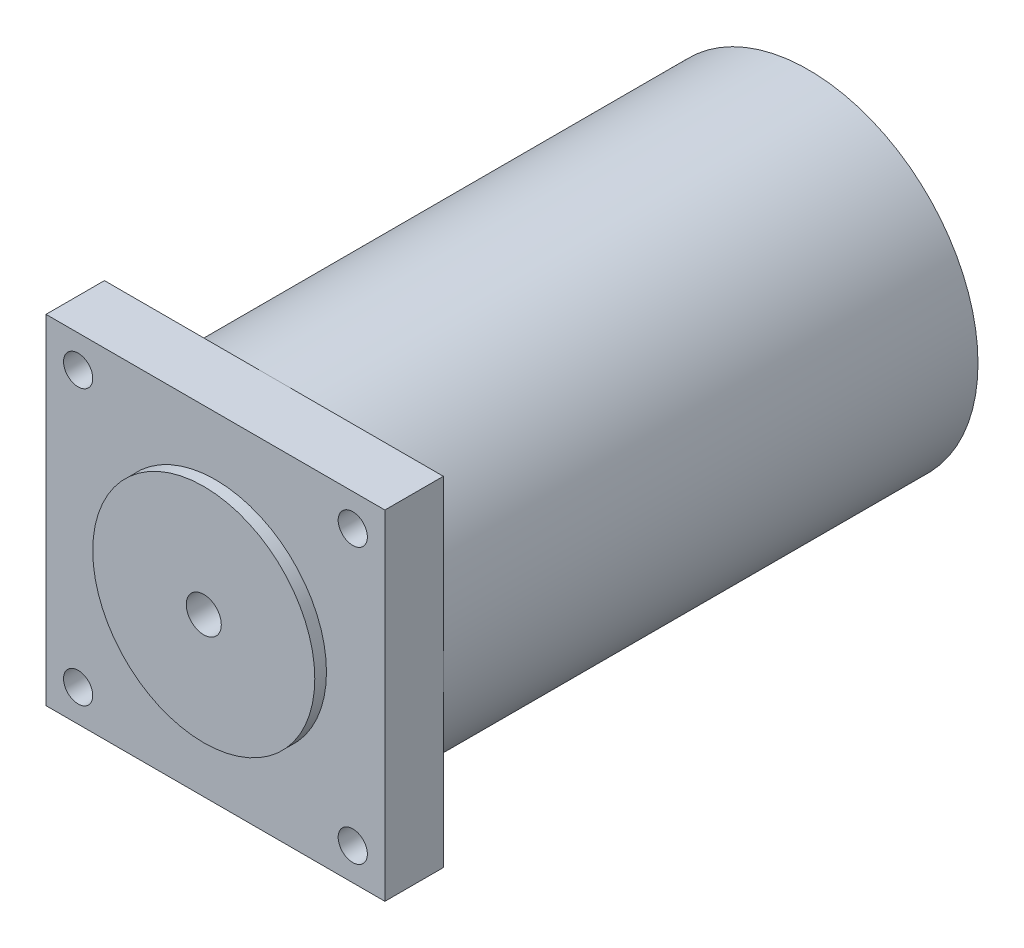
SolidWorks part; units mm, degrees
material "1060 Alloy"
ref_plane "Front Plane" through (0, 0, 0) normal (0, 0, 1) x (1, 0, 0)
ref_plane "Top Plane" through (0, 0, 0) normal (0, 1, 0) x (1, 0, 0)
ref_plane "Right Plane" through (0, 0, 0) normal (1, 0, 0) x (0, 0, -1)
sketch "Sketch1" plane through (0, 0, 0) normal (0, 0, 1) x (1, 0, 0)
  circle A0 centre (0, 0) radius 19
  dimension "D1" = 38
extrude "Boss-Extrude1" add sketch "Sketch1" against normal blind 2
sketch "Sketch3" plane through (0, 0, -2) normal (0, 0, -1) x (-1, 0, 0)
  line L0 (0, 0) -> (-29, 0) construction
  line L1 (-29, 0) -> (-29, 29) construction
  line L3 (-29, 29) -> (29, 29)
  line L4 (-29, 29) -> (-29, -29)
  line L5 (-29, -29) -> (29, -29)
  line L6 (29, 29) -> (29, -29)
  dimension "D1" = 29
  dimension "D2" = 29
  dimension "D3" = 58
extrude "Boss-Extrude2" add sketch "Sketch3" along normal blind 10
sketch "Sketch4" plane through (0, 0, -12) normal (0, 0, -1) x (-1, 0, 0)
  circle A0 centre (0, 0) radius 29
  dimension "D1" = 58
extrude "Boss-Extrude3" add sketch "Sketch4" along normal blind 91.5
sketch "Sketch5" plane through (0, 0, -2) normal (0, 0, 1) x (1, 0, 0)
  line L0 (-29, 29) -> (-29, 23.5) construction
  line L1 (-29, -29) -> (-29, 29) construction
  line L2 (-29, 23.5) -> (-23.5, 23.5) construction
  line L3 (0, 29) -> (0, -29) construction
  line L4 (-29, 29) -> (29, 29) construction
  line L5 (29, -29) -> (-29, -29) construction
  line L6 (-29, 0) -> (29, 0) construction
  circle A0 centre (-23.5, 23.5) radius 2.5
  circle A1 centre (23.5, 23.5) radius 2.5
  circle A2 centre (23.5, -23.5) radius 2.5
  circle A3 centre (-23.5, -23.5) radius 2.5
  dimension "D3" = 5
  dimension "D1" = 5.5
  dimension "D2" = 5.5
extrude "Cut-Extrude1" cut sketch "Sketch5" against normal blind 10
sketch "Sketch6" plane through (0, 0, 0) normal (0, 0, 1) x (1, 0, 0)
  circle A0 centre (0, 0) radius 3
  dimension "D1" = 6
extrude "Cut-Extrude2" cut sketch "Sketch6" against normal blind 12
sketch "Sketch7" plane through (0, 0, 0) normal (1, 0, 0) x (0, 0, -1)
  line L0 (103.5, 0) -> (88.5, 0) construction
  line L1 (103.5, -29) -> (103.5, 29) construction
  circle A0 centre (88.5, 0) radius 1.5
  dimension "D2" = 3
  dimension "D1" = 15
extrude "Cut-Extrude4" cut sketch "Sketch7" against normal through all
